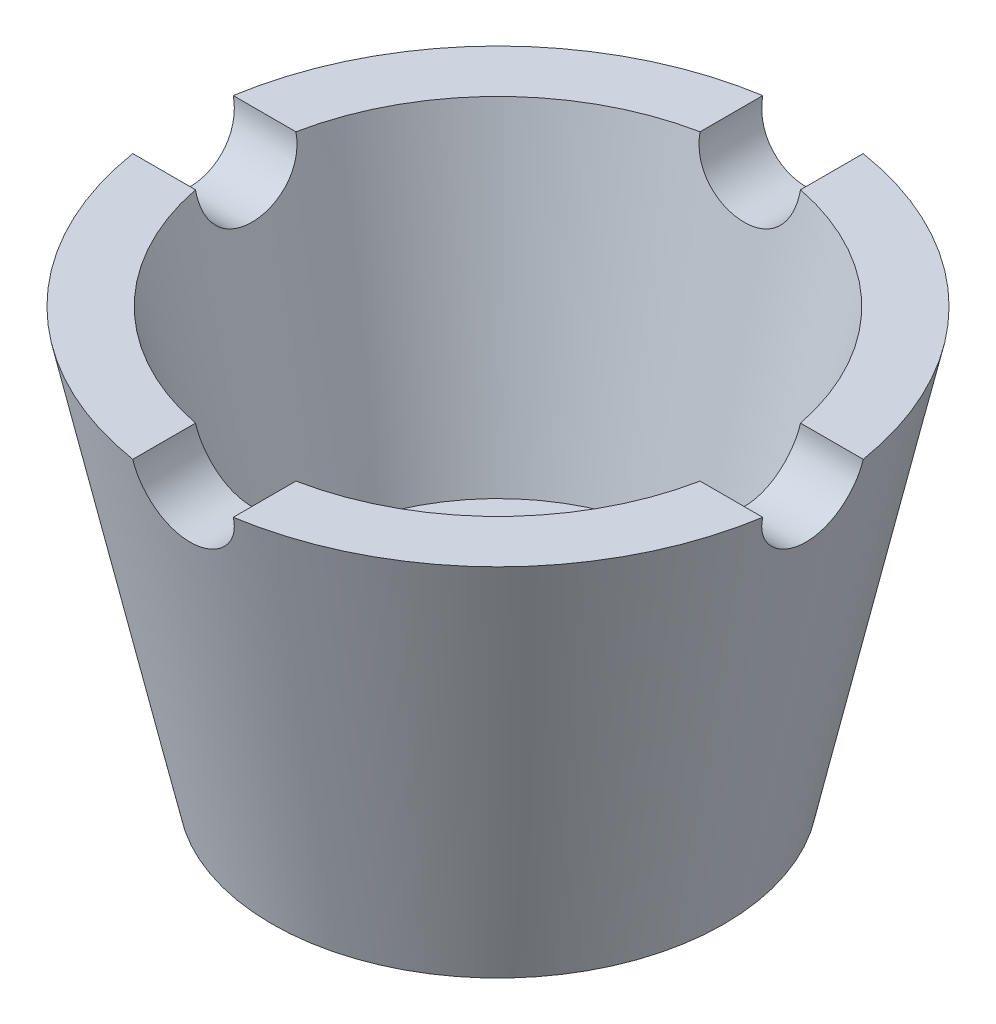
SolidWorks part; units mm, degrees
ref_plane "Front Plane" through (0, 0, 0) normal (0, 0, 1) x (1, 0, 0)
ref_plane "Top Plane" through (0, 0, 0) normal (0, 1, 0) x (1, 0, 0)
ref_plane "Right Plane" through (0, 0, 0) normal (1, 0, 0) x (0, 0, -1)
sketch "Sketch2" plane through (0, 0, 0) normal (0, 0, 1) x (1, 0, 0)
  line L0 (11, 0) -> (22.5, 0)
  line L1 (22.5, 0) -> (31.7537, 42)
  line L2 (31.7537, 42) -> (25.6098, 42)
  line L3 (25.6098, 42) -> (19, 12)
  line L4 (19, 12) -> (11, 12)
  line L5 (11, 12) -> (11, 0)
  line L6 (0, 0) -> (0, 44.8943) construction
  dimension "D1" = 22.5
  dimension "D2" = 11
  dimension "D3" = 12
  dimension "D4" = 42
  dimension "D5" = 19
  dimension "D6" = 6
revolve "Revolve1" add sketch "Sketch2" angle 360 about L6
sketch "Sketch4" plane through (0, 0, 0) normal (0, 0, 1) x (1, 0, 0)
  line L0 (31.7537, 42) -> (-31.7537, 42) construction
  circle A0 centre (0, 42) radius 5
extrude "Cut-Extrude1" cut sketch "Sketch4" against normal blind 40 and the other way blind 39
pattern_circular "CirPattern1" count 4 over 360 about axis through (0, 42, 0) along (0, 1, 0) of "Cut-Extrude1"
